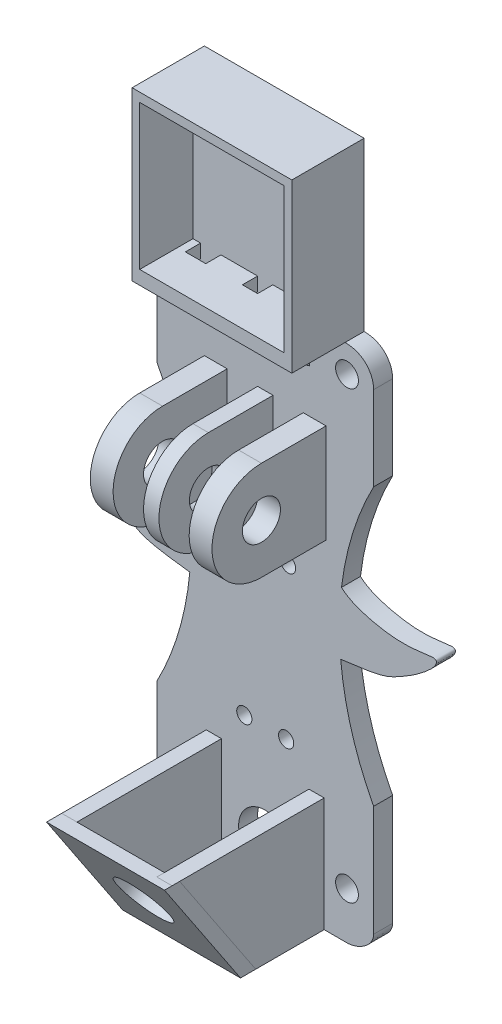
SolidWorks part; units mm, degrees
ref_plane "前视基准面" through (0, 0, 0) normal (0, 0, 1) x (1, 0, 0)
ref_plane "上视基准面" through (0, 0, 0) normal (0, 1, 0) x (1, 0, 0)
ref_plane "右视基准面" through (0, 0, 0) normal (1, 0, 0) x (0, 0, -1)
sketch "Model" plane through (0, 0, 0) normal (0, 0, 1) x (1, 0, 0)
  line L0 (14.6865, 106.179) -> (14.6865, 84.179)
  line L1 (25.1865, 15.9481) -> (35.9365, 15.9481)
  line L2 (35.6865, 106.179) -> (35.6865, 84.179)
  line L3 (39.4365, 80.679) -> (39.4365, 22.179)
  line L4 (39.4365, 22.179) -> (39.4365, 18.679)
  line L5 (25.1865, 15.9481) -> (14.4365, 15.9481)
  line L6 (10.9365, 80.679) -> (10.9365, 22.179)
  line L7 (10.9365, 22.179) -> (10.9365, 18.679)
  line L8 (14.6865, 106.179) -> (35.6865, 106.179)
  circle A0 centre (14.4365, 22.1327) radius 1.5
  circle A1 centre (35.9365, 22.1327) radius 1.5
  circle A2 centre (35.9365, 80.679) radius 1.5
  circle A3 centre (14.4365, 80.679) radius 1.5
  circle A4 centre (25.1865, 25.179) radius 5
  circle A5 centre (27.9365, 35.1327) radius 1
  circle A6 centre (22.4365, 35.1327) radius 1
  spline S0 degree 3 poles (39.4365, 18.679) (39.4365, 17.1993) (37.4163, 15.9481) (35.9365, 15.9481) knots 0 0 0 0 4.439373 4.439373 4.439373 4.439373
  spline S1 degree 3 poles (35.6865, 84.179) (38.1559, 84.179) (39.4365, 82.3889) (39.4365, 80.679) knots 0 0 0 0 5.129571 5.129571 5.129571 5.129571
  spline S2 degree 3 poles (10.9365, 18.679) (10.9365, 17.1993) (12.9567, 15.9481) (14.4365, 15.9481) knots 0 0 0 0 4.439373 4.439373 4.439373 4.439373
  spline S3 degree 3 poles (14.6865, 84.179) (12.2171, 84.179) (10.9365, 82.3889) (10.9365, 80.679) knots 0 0 0 0 5.129571 5.129571 5.129571 5.129571
extrude "凸台-拉伸1" add sketch "Model" along normal blind 2.5
sketch "草图2" plane through (0, 0, 2.5) normal (0, 0, 1) x (1, 0, 0)
  line L0 (14.6865, 106.179) -> (35.6865, 106.179)
  line L2 (35.6865, 106.179) -> (35.6865, 84.179)
  line L3 (15.6865, 105.0116) -> (34.6865, 105.0116)
  line L4 (34.6865, 105.0116) -> (34.6865, 85.9908)
  line L5 (34.6865, 85.9908) -> (15.6865, 85.9908)
  line L6 (15.6865, 85.9908) -> (15.6865, 105.0116)
  line L7 (35.6865, 84.179) -> (14.6865, 84.179)
  line L8 (14.6865, 84.179) -> (14.6865, 106.179)
extrude "凸台-拉伸2" add sketch "草图2" along normal blind 7
sketch "草图3" plane through (0, 0, 2.5) normal (0, 0, 1) x (1, 0, 0)
  line L0 (14.6865, 84.179) -> (35.6865, 84.179) construction
  line L2 (19.3701, 84.179) -> (20.8701, 84.179)
  line L3 (19.3701, 84.179) -> (19.3701, 79.179)
  line L4 (19.3701, 79.179) -> (20.8701, 79.179)
  line L5 (20.8701, 84.179) -> (20.8701, 79.179)
extrude "凸台-拉伸3" add sketch "草图3" along normal blind 7
sketch "草图4" plane through (19.3701, 0, 0) normal (-1, 0, 0) x (0, 0, 1)
  line L0 (9.5, 84.179) -> (2.5, 79.179)
  line L1 (2.5, 80.679) -> (2.5, 18.679) construction
  line L2 (9.5, 79.179) -> (2.5, 79.179) construction
  line L3 (2.5, 79.179) -> (9.5, 79.179)
  line L4 (9.5, 79.179) -> (9.5, 84.179)
extrude "切除-拉伸2" cut sketch "草图4" against normal blind 7
sketch3d "3D草图1"
  line L2 (20.8701, 84.179, 2.5) -> (35.6865, 84.179, 2.5) construction
  line L4 (31.0065, 84.179, 2.5) -> (29.5065, 84.179, 2.5)
  line L5 (31.0065, 84.179, 2.5) -> (31.0065, 79.179, 2.5)
  line L6 (31.0065, 79.179, 2.5) -> (29.5065, 79.179, 2.5)
  line L7 (29.5065, 84.179, 2.5) -> (29.5065, 79.179, 2.5)
extrude "凸台-拉伸6" add sketch "3D草图1" along direction (0, 0, 1) on the side against the normal blind 7
sketch "草图12" plane through (29.5065, 0, 0) normal (-1, 0, 0) x (0, 0, 1)
  line L0 (9.5, 84.179) -> (9.5, 79.179)
  line L1 (9.5, 79.179) -> (2.5, 79.179)
  line L2 (2.5, 79.179) -> (9.5, 84.179)
extrude "切除-拉伸4" cut sketch "草图12" against normal blind 7
sketch "草图13" plane through (0, 84.179, 0) normal (0, -1, 0) x (1, 0, 0)
  line L2 (20.8701, 2.5) -> (29.5065, 2.5) construction
  line L4 (24.1865, 2.5) -> (26.1865, 2.5)
  line L5 (24.1865, 2.5) -> (24.1865, 4.5)
  line L6 (24.1865, 4.5) -> (26.1865, 4.5)
  line L7 (26.1865, 2.5) -> (26.1865, 4.5)
extrude "切除-拉伸5" cut sketch "草图13" against normal blind 7
sketch "草图14" plane through (0, 0, 2.5) normal (0, 0, 1) x (1, 0, 0)
  line L0 (19.4365, 30.9481) -> (19.4365, 17.9481)
  line L1 (14.4365, 15.9481) -> (35.9365, 15.9481) construction
  line L2 (17.4365, 15.9481) -> (17.4365, 30.9481)
  line L3 (17.4365, 30.9481) -> (19.4365, 30.9481)
  line L6 (32.9365, 15.9481) -> (32.9365, 30.9481)
  line L7 (32.9365, 30.9481) -> (30.9365, 30.9481)
  line L12 (30.9365, 30.9481) -> (30.9365, 17.9481)
  line L13 (30.9365, 17.9481) -> (19.4365, 17.9481)
  line L14 (17.4365, 15.9481) -> (32.9365, 15.9481)
extrude "凸台-拉伸7" add sketch "草图14" along normal blind 20
sketch "草图15" plane through (17.4365, 0, 0) normal (-1, 0, 0) x (0, 0, 1)
  line L1 (22.5, 30.9481) -> (22.5, 15.9481)
  line L2 (22.5, 15.9481) -> (12.5, 15.9481)
  line L3 (22.5, 15.9481) -> (2.5, 15.9481) construction
  line L4 (12.5, 15.9481) -> (22.5, 30.9481)
extrude "切除-拉伸6" cut sketch "草图15" against normal blind 20
sketch "草图16" plane through (0, -0.8621, 1.2932) normal (0, -0.5547, 0.8321) x (1, 0, 0)
sketch "草图19" plane through (0, -0.8621, 1.2932) normal (0, -0.5547, 0.8321) x (1, 0, 0)
  line L17 (32.9365, 38.2311) -> (30.9365, 38.2311)
  line L18 (30.9365, 38.2311) -> (30.9365, 22.6071)
  line L19 (30.9365, 22.6071) -> (19.4365, 22.6071)
  line L20 (19.4365, 22.6071) -> (19.4365, 38.2311)
  line L21 (19.4365, 38.2311) -> (17.4365, 38.2311)
  line L22 (17.4365, 38.2311) -> (17.4365, 20.2034)
  line L23 (17.4365, 20.2034) -> (32.9365, 20.2034)
  line L24 (32.9365, 20.2034) -> (32.9365, 38.2311)
  line L25 (32.9365, 38.2311) -> (30.9365, 38.2311)
  line L30 (17.4365, 38.2311) -> (17.4365, 20.2034)
  line L31 (17.4365, 20.2034) -> (32.9365, 20.2034)
  line L32 (32.9365, 20.2034) -> (32.9365, 38.2311)
  dimension "D1" = 0
sketch "草图20" plane through (0, -0.8621, 1.2932) normal (0, -0.5547, 0.8321) x (1, 0, 0)
  line L0 (17.4365, 38.2311) -> (32.9365, 38.2311)
  line L1 (32.9365, 38.2311) -> (32.9365, 20.2034)
  line L2 (32.9365, 20.2034) -> (17.4365, 20.2034)
  line L3 (17.4365, 20.2034) -> (17.4365, 38.2311)
extrude "凸台-拉伸9" add sketch "草图20" along direction (0, 0, -1) on the side against the normal mid plane 2 separate body
sketch "草图21" plane through (0, -1.3237, 1.9855) normal (0, -0.5547, 0.8321) x (1, 0, 0)
  circle A0 centre (25.1865, 29.772) radius 3.5
extrude "切除-拉伸7" cut sketch "草图21" against normal blind 2
sketch "草图22" plane through (0, 0, 2.5) normal (0, 0, 1) x (1, 0, 0)
sketch "草图23" plane through (0, 0, 2.5) normal (0, 0, 1) x (1, 0, 0)
  circle A0 centre (25.1865, 22.179) radius 3.5
extrude "切除-拉伸8" cut sketch "草图23" against normal blind 4
sketch "草图25" plane through (0, 0, 2.5) normal (0, 0, 1) x (1, 0, 0)
  line L1 (25.1865, 73.429) -> (26.2145, 73.429)
  line L2 (26.2145, 73.429) -> (26.2145, 60.429)
  line L3 (26.2145, 60.429) -> (24.1865, 60.429)
  line L4 (24.1865, 60.429) -> (24.1865, 73.429)
  line L5 (24.1865, 73.429) -> (25.1865, 73.429)
  line L7 (30.1865, 73.429) -> (33.1865, 73.429)
  line L8 (33.1865, 73.429) -> (33.1865, 60.429)
  line L11 (30.1865, 73.429) -> (30.1865, 60.429)
  line L12 (30.1865, 60.429) -> (33.1865, 60.429)
  line L13 (20.1865, 60.429) -> (17.1865, 60.429)
  line L14 (17.1865, 73.429) -> (17.1865, 60.429)
  line L15 (20.1865, 73.429) -> (17.1865, 73.429)
  line L16 (20.1865, 73.429) -> (20.1865, 60.429)
extrude "凸台-拉伸10" add sketch "草图25" along normal blind 15
sketch "草图26" plane through (17.1865, 0, 0) normal (-1, 0, 0) x (0, 0, 1)
  circle A0 centre (11, 66.929) radius 2.5
extrude "切除-拉伸9" cut sketch "草图26" against normal blind 18
sketch "草图27" plane through (17.1865, 0, 0) normal (-1, 0, 0) x (0, 0, 1)
  line L0 (17.5, 73.429) -> (2.5, 73.429) construction
  line L1 (11, 73.429) -> (11, 75.5365)
  line L2 (11, 75.5365) -> (21.7471, 75.5365)
  line L3 (21.7471, 75.5365) -> (21.7471, 59.0459)
  line L4 (21.7471, 59.0459) -> (11, 59.4314)
  line L5 (11, 59.4314) -> (11, 60.429)
  arc A0 (11, 73.429) -> (11, 60.429) centre (11, 66.929) cw
  circle A1 centre (11, 66.929) radius 2.5 construction
extrude "切除-拉伸10" cut sketch "草图27" against normal blind 16
sketch "草图28" plane through (0, 84.179, 0) normal (0, -1, 0) x (1, 0, 0)
  line L1 (14.4365, 2.5) -> (17.4365, 2.5) construction
  line L2 (16.6865, 2.5) -> (16.6865, 4.5)
  line L3 (16.6865, 4.5) -> (19.3701, 4.5)
  line L4 (19.3701, 4.5) -> (19.3701, 2.5)
  line L5 (17.4365, 2.5) -> (19.4365, 2.5) construction
  line L6 (14.6865, 2.5) -> (19.3701, 2.5) construction
  line L7 (19.3701, 2.5) -> (16.6865, 2.5)
  line L11 (31.0014, 2.4958) -> (33.6851, 2.4938)
  line L12 (31.0029, 4.4958) -> (31.0014, 2.4958)
  line L13 (33.6851, 2.4938) -> (33.6865, 4.4938)
  line L14 (33.6865, 4.4938) -> (31.0029, 4.4958)
  line L15 (31.0029, 4.4958) -> (33.6865, 4.4938)
  line L16 (33.6851, 2.4938) -> (31.0014, 2.4958)
sketch "草图29" plane through (0, 84.179, 0) normal (0, -1, 0) x (1, 0, 0)
extrude "切除-拉伸12" cut sketch "草图28" against normal blind 2 contours L3 L4 L7 L2 | L14 L12 L11 L13
sketch "草图30" plane through (0, 0, 2.5) normal (0, 0, 1) x (1, 0, 0)
  circle A0 centre (28.1883, 55.179) radius 1
  circle A2 centre (22.1883, 54.179) radius 1
extrude "切除-拉伸13" cut sketch "草图30" against normal blind 10
sketch "草图31" plane through (0, 0, 2.5) normal (0, 0, 1) x (1, 0, 0)
  circle A0 centre (-23.5635, 51.429) radius 39
  circle A1 centre (73.9365, 51.429) radius 39
extrude "切除-拉伸14" cut sketch "草图31" against normal blind 10
sketch "草图32" plane through (0, 0, 2.5) normal (0, 0, 1) x (1, 0, 0)
  line L0 (17.2145, 60.429) -> (15.2974, 47.8229)
  line L5 (33.1865, 60.429) -> (35.1036, 47.8229)
  arc A1 (39.4365, 69.6156) -> (39.4365, 33.2425) centre (73.9365, 51.429) ccw construction
  spline S0 degree 3 poles (33.1865, 60.429) (33.9982, 57.2618) (34.5214, 55.0305) (44.3629, 53.3009) (47.8, 54.5625) (47.6334, 53.0148) (45.2472, 51.1375) (41.1508, 48.687) (40.6479, 48.5267) (35.1036, 47.8229) knots 0 0 0 0 0.228684 0.270207 0.399122 0.431668 0.563126 0.621603 1 1 1 1
  spline S1 degree 3 poles (17.2145, 60.429) (16.4028, 57.2618) (15.8796, 55.0305) (6.0382, 53.3009) (2.601, 54.5625) (2.7677, 53.0148) (5.1538, 51.1375) (9.2503, 48.687) (9.7531, 48.5267) (15.2974, 47.8229) knots 0 0 0 0 0.228684 0.270207 0.399122 0.431668 0.563126 0.621603 1 1 1 1
sketch "草图33" plane through (0, 0, 2.5) normal (0, 0, 1) x (1, 0, 0)
  circle A0 centre (22.4365, 35.1327) radius 1
  circle A1 centre (27.9365, 35.1327) radius 1
extrude "切除-拉伸15" cut sketch "草图33" against normal blind 2.5
extrude "凸台-拉伸13" add sketch "草图32" against normal blind 2.5
